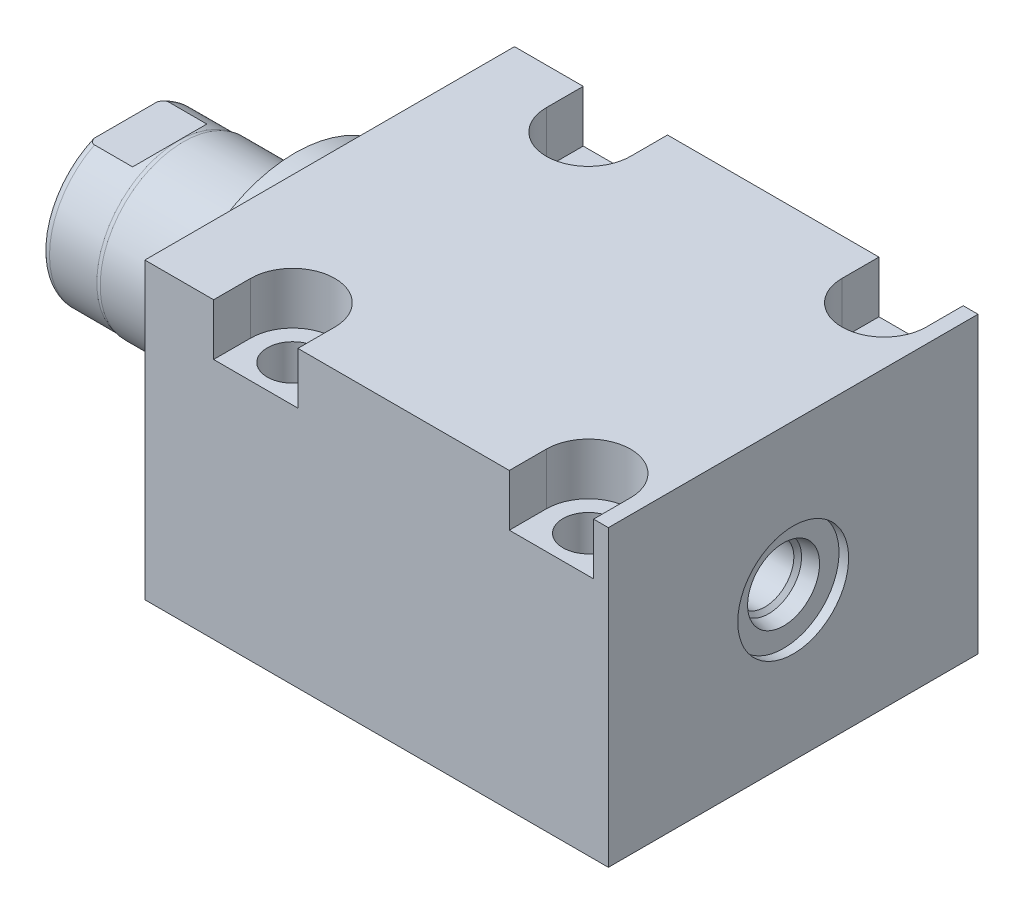
SolidWorks part; units mm, degrees
material "Alloy Steel"
ref_plane "Front Plane" through (0, 0, 0) normal (0, 0, 1) x (1, 0, 0)
ref_plane "Top Plane" through (0, 0, 0) normal (0, 1, 0) x (1, 0, 0)
ref_plane "Right Plane" through (0, 0, 0) normal (1, 0, 0) x (0, 0, -1)
ref_plane "Plane1" through (0, 0, 0) normal (1, 0, 0) x (0, 0, -1)
sketch "Sketch1" plane through (0, 0, 0) normal (1, 0, 0) x (0, 0, -1)
  line L0 (-31.75, 25.146) -> (31.75, 25.146)
  line L1 (31.75, 25.146) -> (31.75, -25.4)
  line L2 (31.75, -25.4) -> (-31.75, -25.4)
  line L3 (-31.75, -25.4) -> (-31.75, 25.146)
  line L4 (0, -24.4475) -> (0, 24.4475) construction
  dimension "D1" = 50.546
  dimension "D2" = 25.4
  dimension "D3" = 63.5
  dimension "D4" = 31.75
extrude "Extrude1" add sketch "Sketch1" along normal blind 79.629
sketch "Sketch5" plane through (0, 0, 0) normal (-1, 0, 0) x (0, 0, 1)
  circle A0 centre (0, 0) radius 22.225
  dimension "D1" = 44.45
extrude "Extrude2" add sketch "Sketch5" along normal blind 5.969
ref_plane "Plane5" through (0, 0, 0) normal (0, -1, 0) x (0, 0, 1)
sketch "Sketch6" plane through (0, 0, 0) normal (0, -1, 0) x (0, 0, 1)
  line L0 (0, 5.969) -> (-14.2875, 5.969)
  line L1 (-14.2875, 5.969) -> (-14.2875, 35.052)
  line L2 (-14.2875, 35.052) -> (0, 35.052)
  line L3 (0, 35.052) -> (0, 5.969)
  line L4 (0, -5.7546) -> (0, 21.1709) construction
  line L5 (22.225, 5.969) -> (-22.225, 5.969) construction
  line L6 (31.75, -79.629) -> (-31.75, -79.629) construction
  dimension "D1" = 114.681
  dimension "D2" = 28.575
revolve "Revolve1" add sketch "Sketch6" angle 360 about L4
ref_plane "Plane6" through (-18.5113, 3.2639, 0) normal (0, 0, 1) x (0, 1, 0)
sketch "S2D0001" plane through (-18.5113, 3.2639, 0) normal (0, 0, 1) x (0, 1, 0)
  line L0 (2.286, 14.473) -> (2.286, -1.9505)
  line L2 (3.4798, 16.5407) -> (-3.2639, 16.5407)
  line L3 (-3.2639, 16.5407) -> (-3.2639, -1.9505)
  line L4 (2.286, 14.473) -> (3.4798, 16.5407)
  line L5 (-3.2639, -18.5113) -> (-3.2639, 2.765) construction
  line L6 (11.0236, 16.5407) -> (-17.5514, 16.5407) construction
  line L7 (2.286, -1.9505) -> (-3.2639, -1.9505)
  dimension "D1" = 30
  dimension "D2" = 13.4874
  dimension "D3" = 11.0998
  dimension "D4" = 18.4912
revolve "Cut-Revolve4" cut sketch "S2D0001" angle 360 about L5
ref_plane "Plane7" through (0, 0, 0) normal (0, 1, 0) x (0, 0, -1)
sketch "Sketch8" plane through (0, 0, 0) normal (0, 1, 0) x (0, 0, -1)
  line L0 (-14.2875, 25.146) -> (-14.097, 25.908)
  line L1 (-14.097, 25.908) -> (-14.097, 34.036)
  line L2 (0, 12.6594) -> (0, 20.8178) construction
  line L3 (-14.2875, 25.146) -> (-14.2875, 35.052)
  line L4 (-13.7089, 35.052) -> (-14.2875, 35.052)
  line L5 (14.2875, 35.052) -> (-14.2875, 35.052) construction
  line L6 (-14.2875, 35.052) -> (-14.2875, 5.969) construction
  arc A0 (-13.7089, 35.052) -> (-14.097, 34.036) centre (-12.573, 34.036) ccw
  dimension "D2" = 1.524
  dimension "D1" = 28.194
  dimension "D3" = 1.016
  dimension "D4" = 0.762
  dimension "D5" = 9.144
revolve "Cut-Revolve5" cut sketch "Sketch8" angle 360 about L2
ref_plane "Plane11" through (0, 0, 0) normal (0, 0, -1) x (0, -1, 0)
sketch "Sketch12" plane through (0, 0, 0) normal (0, 0, -1) x (0, -1, 0)
  line L0 (12.573, 35.052) -> (12.573, 27.4828)
  line L1 (12.573, 27.4828) -> (14.097, 25.9588)
  line L2 (-12.573, 35.052) -> (-12.573, 27.4828)
  line L3 (-12.573, 27.4828) -> (-14.097, 25.9588)
  line L4 (12.573, 35.052) -> (14.097, 35.052)
  line L5 (0, 13.7262) -> (0, 20.767) construction
  line L6 (-14.097, 25.9588) -> (-14.097, 35.052)
  line L8 (14.097, 25.908) -> (14.097, 34.036) construction
  line L9 (14.097, 25.9588) -> (14.097, 35.052)
  line L10 (-12.573, 35.052) -> (-14.097, 35.052)
  line L12 (13.7089, 35.052) -> (-13.7089, 35.052) construction
  dimension "D1" = 25.146
  dimension "D2" = 7.5692
  dimension "D3" = 45
extrude "Cut-Extrude4" cut sketch "Sketch12" against normal mid plane 60.96
hole_wizard "Hole2" positions "Sketch17" profile "Sketch16" legacy
sketch "Sketch17" plane through (0, 25.146, 0) normal (0, 1, 0) x (-1, 0, 0)
  line L0 (0, 0) -> (-59.3363, 0) construction
  line L1 (0, -31.75) -> (0, 31.75) construction
  point P0 (-19.05, -25.4)
  point P9 (-19.05, 25.4)
  dimension "D1" = 50.8
  dimension "D2" = 19.05
sketch "Sketch16" plane through (19.05, 25.146, -25.4) normal (1, 0, 0) x (0, 0, 1)
  line L0 (0, 0) -> (0, 50.546)
  line L1 (0, 50.546) -> (4.3688, 50.546)
  line L2 (4.3688, 50.546) -> (4.3688, 0)
  line L3 (4.3688, 0) -> (0, 0)
  line L4 (0, 110) -> (0, -10) construction
  dimension "Diameter" = 8.7376
  dimension "Depth" = 50.546
pattern_linear "LPattern1" count 2 spacing 50.8 along (1, 0, 0) of "Hole2"
sketch "Sketch18" plane through (0, 25.146, 0) normal (0, 1, 0) x (1, 0, 0)
  line L0 (0, 0) -> (50.053, 0) construction
  line L2 (79.629, -31.75) -> (0, -31.75) construction
  line L4 (77.089, -31.75) -> (62.611, -31.75)
  line L5 (11.811, -25.4) -> (11.811, -31.75)
  line L6 (26.289, -25.4) -> (26.289, -31.75)
  line L7 (62.611, -25.4) -> (62.611, -31.75)
  line L8 (77.089, 25.4) -> (77.089, 31.75)
  line L9 (26.289, -31.75) -> (11.811, -31.75)
  line L12 (26.289, 31.75) -> (11.811, 31.75)
  line L14 (62.611, 25.4) -> (62.611, 31.75)
  line L15 (26.289, 25.4) -> (26.289, 31.75)
  line L16 (11.811, 25.4) -> (11.811, 31.75)
  line L17 (77.089, 31.75) -> (62.611, 31.75)
  line L18 (77.089, -25.4) -> (77.089, -31.75)
  arc A0 (26.289, -25.4) -> (11.811, -25.4) centre (19.05, -25.4) ccw
  arc A1 (77.089, -25.4) -> (62.611, -25.4) centre (69.85, -25.4) ccw
  arc A2 (77.089, 25.4) -> (62.611, 25.4) centre (69.85, 25.4) cw
  arc A3 (26.289, 25.4) -> (11.811, 25.4) centre (19.05, 25.4) cw
  dimension "D1" = 14.478
extrude "Cut-Extrude5" cut sketch "Sketch18" against normal blind 8.89
hole_wizard "Hole3" positions "Sketch20" profile "Sketch19" legacy
sketch "Sketch20" plane through (0, -25.4, 0) normal (0, -1, 0) x (1, 0, 0)
  line L0 (0, 31.75) -> (0, -31.75) construction
  point P0 (12.7, 0)
  dimension "D1" = 12.7
sketch "Sketch19" plane through (12.7, -25.4, 0) normal (1, 0, 0) x (0, 0, -1)
  line L0 (0, 0) -> (0, 10.4789)
  line L1 (0, 10.4789) -> (1.5875, 9.525)
  line L2 (1.5875, 9.525) -> (1.5875, 1.4478)
  line L3 (1.5875, 1.4478) -> (5.6705, 1.4478)
  line L4 (5.6705, 0) -> (0, 0)
  line L5 (0, -11.3109) -> (0, 121.1557) construction
  line L6 (0, 10.4789) -> (-1.5875, 9.525) construction
  line L7 (5.6705, 1.4478) -> (5.6705, 0)
  dimension "Depth" = 9.525
  dimension "Drill Angle" = 118
  dimension "Diameter" = 3.175
  dimension "C-Bore Diameter" = 11.3411
  dimension "C-Bore Depth" = 1.4478
hole_wizard "Hole4" positions "Sketch21" profile "Sketch22" legacy
sketch "Sketch21" plane through (0, -25.4, 0) normal (0, -1, 0) x (1, 0, 0)
  point P0 (63.5, 0)
  dimension "D1" = 50.8
sketch "Sketch22" plane through (63.5, -25.4, 0) normal (1, 0, 0) x (0, 0, -1)
  line L0 (0, 0) -> (0, 10.4789)
  line L1 (0, 10.4789) -> (1.5875, 9.525)
  line L2 (1.5875, 9.525) -> (1.5875, 1.4478)
  line L3 (1.5875, 1.4478) -> (5.6705, 1.4478)
  line L4 (5.6705, 0) -> (0, 0)
  line L5 (0, -11.3109) -> (0, 121.1557) construction
  line L6 (0, 10.4789) -> (-1.5875, 9.525) construction
  line L7 (5.6705, 1.4478) -> (5.6705, 0)
  dimension "Depth" = 9.525
  dimension "Drill Angle" = 118
  dimension "Diameter" = 3.175
  dimension "C-Bore Diameter" = 11.3411
  dimension "C-Bore Depth" = 1.4478
chamfer "Chamfer1" distance 0.635 angle 45 2 edges at (63.5, -23.9522, -1.5875) (12.7, -23.9522, -1.5875)
sketch "Sketch23" plane through (0, 0, 0) normal (0, 0, 1) x (1, 0, 0)
  line L0 (12.7, -23.9522) -> (12.7, -21.4272) construction
  line L1 (10.4775, -23.9522) -> (14.9225, -23.9522) construction
  line L2 (7.0294, -23.9522) -> (18.3705, -23.9522) construction
  line L3 (7.0294, -23.9522) -> (7.0294, -25.4) construction
  circle A0 centre (8.4772, -25.4) radius 1.4478
  dimension "D1" = 2.8956
revolve "Revolve2" add sketch "Sketch23" angle 360 about L0
pattern_linear "LPattern3" count 2 spacing 50.8 along (1, 0, 0) of bodies 128
sketch "Sketch24" plane through (0, 0, 0) normal (0, 0, 1) x (1, 0, 0)
  line L0 (0, 0) -> (74.772, 0) construction
  line L1 (79.629, 9.525) -> (77.978, 9.525)
  line L2 (79.629, 25.146) -> (79.629, -25.4) construction
  line L3 (77.978, 9.525) -> (77.978, 6.1849)
  line L4 (77.978, 6.1849) -> (75.4253, 5.6423)
  line L5 (75.4253, 5.6423) -> (74.7614, 4.9784)
  line L6 (74.7614, 4.9784) -> (63.373, 4.9784)
  line L7 (63.373, 4.9784) -> (63.373, 0)
  line L8 (63.373, 0) -> (79.629, 0)
  line L9 (79.629, 0) -> (79.629, 9.525)
  dimension "D1" = 1.651
  dimension "D2" = 19.05
  dimension "D3" = 9.9568
  dimension "D4" = 16.256
  dimension "D5" = 12
  dimension "D6" = 45
  dimension "D7" = 12.3698
  dimension "D8" = 2.5527
revolve "Cut-Revolve6" cut sketch "Sketch24" angle 360 about L0
